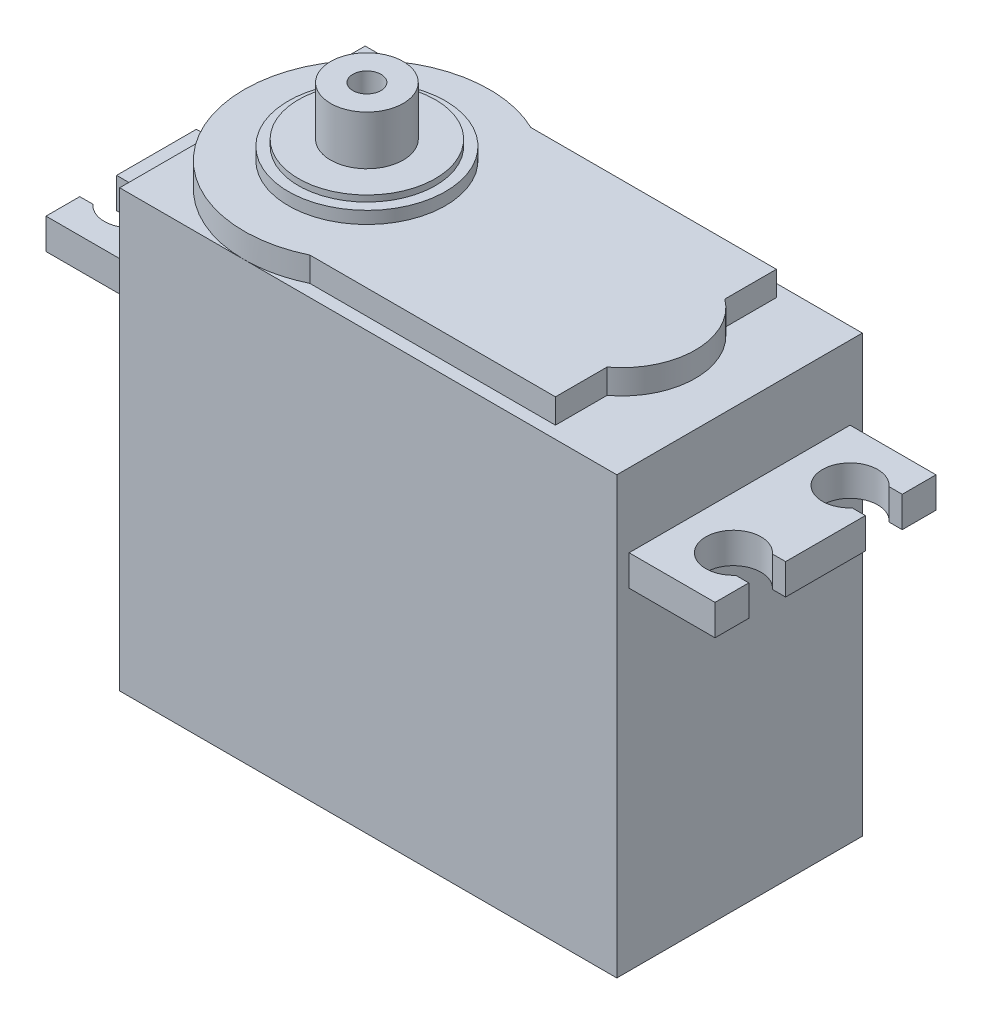
SolidWorks part; units mm, degrees
ref_plane "Plano frontal" through (0, 0, 0) normal (0, 0, 1) x (1, 0, 0)
ref_plane "Plano superior" through (0, 0, 0) normal (0, 1, 0) x (1, 0, 0)
ref_plane "Plano direito" through (0, 0, 0) normal (1, 0, 0) x (0, 0, -1)
ref_plane "Plano1" through (0, 0, -10) normal (0, 0, -1) x (-1, 0, 0)
sketch "Esboço1" plane through (0, 0, -10) normal (0, 0, -1) x (-1, 0, 0)
  line L0 (20.25, 0) -> (20.25, 35.5)
  line L1 (20.25, 35.5) -> (-20.25, 35.5)
  line L2 (-20.25, 35.5) -> (-20.25, 0)
  line L3 (-20.25, 0) -> (20.25, 0)
extrude "Ressalto-extrusão1" add sketch "Esboço1" against normal blind 20
sketch "Esboço2" plane through (0, 35.5, 0) normal (0, 1, 0) x (-1, 0, 0)
  line L0 (-14.25, 9) -> (5.75, 9)
  line L1 (5.75, -9) -> (-14.25, -9)
  line L2 (-14.25, -9) -> (-14.25, 9)
  arc A0 (5.75, 9) -> (5.75, -9) centre (10.1089, 0) cw
extrude "Ressalto-extrusão2" add sketch "Esboço2" along normal blind 2
sketch "Esboço3" plane through (20.25, 0, 0) normal (1, 0, 0) x (0, 0, -1)
  line L0 (-9, 27) -> (-9, 29.5)
  line L1 (-9, 29.5) -> (9, 29.5)
  line L2 (9, 29.5) -> (9, 27)
  line L3 (9, 27) -> (-9, 27)
extrude "Ressalto-extrusão3" add sketch "Esboço3" along normal blind 7
sketch "Esboço4" plane through (0, 27, 0) normal (0, -1, 0) x (1, 0, 0)
  line L0 (27.25, 3.25) -> (27.25, 6.25)
  line L1 (27.25, 6.25) -> (26.1771, 6.25)
  line L2 (26.1771, 3.25) -> (27.25, 3.25)
  arc A0 (26.1771, 6.25) -> (26.1771, 3.25) centre (24.5, 4.75) cw
extrude "Corte-extrusão1" cut sketch "Esboço4" against normal through all
sketch "Esboço5" plane through (0, 27, 0) normal (0, -1, 0) x (1, 0, 0)
  line L0 (27.25, -6.25) -> (27.25, -3.25)
  line L1 (27.25, -3.25) -> (26.1771, -3.25)
  line L2 (26.1771, -6.25) -> (27.25, -6.25)
  arc A0 (26.1771, -3.25) -> (26.1771, -6.25) centre (24.5, -4.75) cw
extrude "Corte-extrusão2" cut sketch "Esboço5" against normal through all
sketch "Esboço6" plane through (0, 35.5, 0) normal (0, 1, 0) x (-1, 0, 0)
  line L0 (-14.25, 4.8) -> (-14.25, -4.8)
  arc A0 (-14.25, -4.8) -> (-14.25, 4.8) centre (-10.65, 0) cw
extrude "Ressalto-extrusão4" add sketch "Esboço6" along normal blind 2
sketch "Esboço7" plane through (-20.25, 0, 0) normal (-1, 0, 0) x (0, 0, 1)
  line L0 (9, 29.5) -> (9, 27)
  line L1 (9, 27) -> (-9, 27)
  line L2 (-9, 27) -> (-9, 29.5)
  line L3 (-9, 29.5) -> (9, 29.5)
extrude "Ressalto-extrusão5" add sketch "Esboço7" along normal blind 7
sketch "Esboço8" plane through (0, 29.5, 0) normal (0, 1, 0) x (-1, 0, 0)
  line L0 (27.25, 6.25) -> (26.1771, 6.25)
  line L1 (26.1771, 3.25) -> (27.25, 3.25)
  line L2 (27.25, 3.25) -> (27.25, 6.25)
  arc A0 (26.1771, 6.25) -> (26.1771, 3.25) centre (24.5, 4.75) cw
extrude "Corte-extrusão3" cut sketch "Esboço8" against normal through all
sketch "Esboço9" plane through (0, 29.5, 0) normal (0, 1, 0) x (-1, 0, 0)
  line L0 (27.25, -6.25) -> (27.25, -3.25)
  line L1 (27.25, -3.25) -> (26.1771, -3.25)
  line L2 (26.1771, -6.25) -> (27.25, -6.25)
  arc A0 (26.1771, -3.25) -> (26.1771, -6.25) centre (24.5, -4.75) cw
extrude "Corte-extrusão4" cut sketch "Esboço9" against normal through all
ref_plane "Plano2" through (0, 0, 4.75) normal (0, 0, 1) x (1, 0, 0)
sketch "Esboço10" plane through (0, 0, 4.75) normal (0, 0, 1) x (1, 0, 0)
  line L0 (-22.25, 29.5) -> (-24.5, 29.5)
  line L1 (-24.5, 29.5) -> (-24.5, 27)
  line L2 (-24.5, 27) -> (-22.25, 27)
  line L3 (-22.25, 27) -> (-22.25, 29.5)
  line L4 (-24.5, 29.5) -> (-24.5, 27) construction
revolve "Corte-Revolução1" cut sketch "Esboço10" angle 360 about L4
ref_plane "Plano3" through (0, 0, -4.75) normal (0, 0, 1) x (1, 0, 0)
sketch "Esboço11" plane through (0, 0, -4.75) normal (0, 0, 1) x (1, 0, 0)
  line L0 (-22.25, 29.5) -> (-24.5, 29.5)
  line L1 (-24.5, 29.5) -> (-24.5, 27)
  line L2 (-24.5, 27) -> (-22.25, 27)
  line L3 (-22.25, 27) -> (-22.25, 29.5)
  line L4 (-24.5, 29.5) -> (-24.5, 27) construction
revolve "Corte-Revolução2" cut sketch "Esboço11" angle 360 about L4
sketch "Esboço12" plane through (0, 0, -4.75) normal (0, 0, 1) x (1, 0, 0)
  line L0 (26.75, 29.5) -> (24.5, 29.5)
  line L1 (24.5, 29.5) -> (24.5, 27)
  line L2 (24.5, 27) -> (26.75, 27)
  line L3 (26.75, 27) -> (26.75, 29.5)
  line L4 (24.5, 29.5) -> (24.5, 27) construction
revolve "Corte-Revolução3" cut sketch "Esboço12" angle 360 about L4
sketch "Esboço13" plane through (0, 0, 4.75) normal (0, 0, 1) x (1, 0, 0)
  line L0 (26.75, 29.5) -> (24.5, 29.5)
  line L1 (24.5, 29.5) -> (24.5, 27)
  line L2 (24.5, 27) -> (26.75, 27)
  line L3 (26.75, 27) -> (26.75, 29.5)
  line L4 (24.5, 29.5) -> (24.5, 27) construction
revolve "Corte-Revolução4" cut sketch "Esboço13" angle 360 about L4
sketch "Esboço14" plane through (0, 0, 0) normal (0, 0, 1) x (1, 0, 0)
  line L0 (-4.5339, 39) -> (-10.1089, 39)
  line L1 (-10.1089, 39) -> (-10.1089, 37.5)
  line L2 (-10.1089, 37.5) -> (-3.7089, 37.5)
  line L3 (-3.7089, 37.5) -> (-3.7089, 38.5)
  line L4 (-3.7089, 38.5) -> (-4.5339, 38.5)
  line L5 (-4.5339, 38.5) -> (-4.5339, 39)
  line L6 (-10.1089, 39) -> (-10.1089, 37.5) construction
revolve "Revolução1" add sketch "Esboço14" angle 360 about L6
sketch "Esboço15" plane through (0, 39, 0) normal (0, 1, 0) x (1, 0, 0)
  circle A0 centre (-10.1089, 0) radius 2.96
  circle A1 centre (-10.1089, 0) radius 1.15
extrude "Ressalto-extrusão6" add sketch "Esboço15" along normal blind 4
